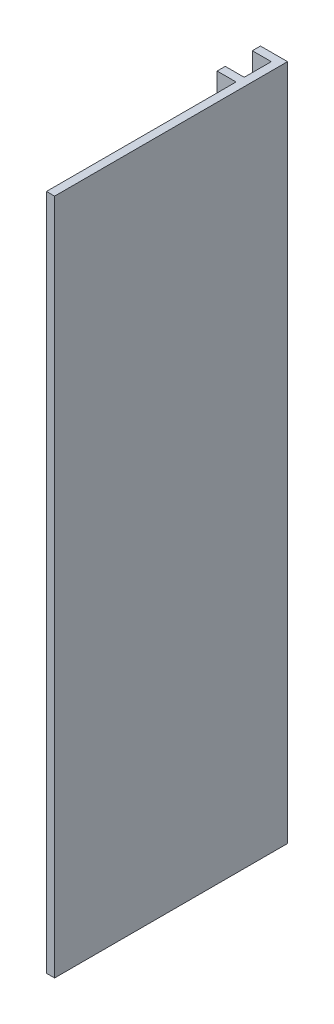
SolidWorks part; units mm, degrees
ref_plane "Front Plane" through (0, 0, 0) normal (0, 0, 1) x (1, 0, 0)
ref_plane "Top Plane" through (0, 0, 0) normal (0, 1, 0) x (1, 0, 0)
ref_plane "Right Plane" through (0, 0, 0) normal (1, 0, 0) x (0, 0, -1)
sketch "Sketch2" plane through (0, 0, 0) normal (0, 1, 0) x (1, 0, 0)
  line L0 (-1.1333, 63.7609) -> (8.8667, 63.7609)
  line L1 (8.8667, 63.7609) -> (8.8667, -22.2391)
  line L2 (8.8667, -22.2391) -> (5.8667, -22.2391)
  line L3 (5.8667, -22.2391) -> (5.8667, 47.7609)
  line L4 (5.8667, 47.7609) -> (-1.1333, 47.7609)
  line L5 (-1.1333, 47.7609) -> (-1.1333, 50.7609)
  line L6 (-1.1333, 50.7609) -> (5.8667, 50.7609)
  line L7 (5.8667, 50.7609) -> (5.8667, 60.7609)
  line L8 (5.8667, 60.7609) -> (-1.1333, 60.7609)
  line L9 (-1.1333, 60.7609) -> (-1.1333, 63.7609)
  dimension "D1" = 3
  dimension "D2" = 3
  dimension "D3" = 10
  dimension "D4" = 3
  dimension "D5" = 10
  dimension "D6" = 7
  dimension "D7" = 7
  dimension "D8" = 70
extrude "Boss-Extrude1" add sketch "Sketch2" along normal blind 250
